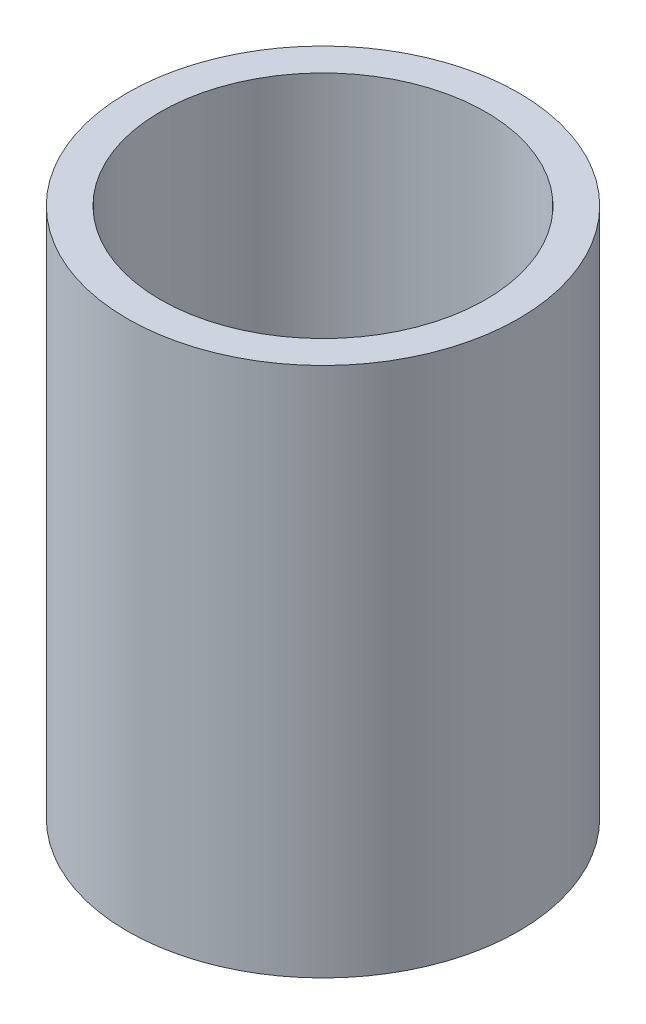
SolidWorks part; units mm, degrees
material "6061 Alloy"
ref_plane "Front Plane" through (0, 0, 0) normal (0, 0, 1) x (1, 0, 0)
ref_plane "Top Plane" through (0, 0, 0) normal (0, 1, 0) x (1, 0, 0)
ref_plane "Right Plane" through (0, 0, 0) normal (1, 0, 0) x (0, 0, -1)
sketch "Sketch1" plane through (0, 0, 0) normal (0, 1, 0) x (1, 0, 0)
  circle A0 centre (0, 0) radius 21.082
  circle A1 centre (0, 0) radius 17.526
  dimension "D1" = 42.164
  dimension "D2" = 35.052
extrude "Boss-Extrude1" add sketch "Sketch1" along normal blind 57.15
